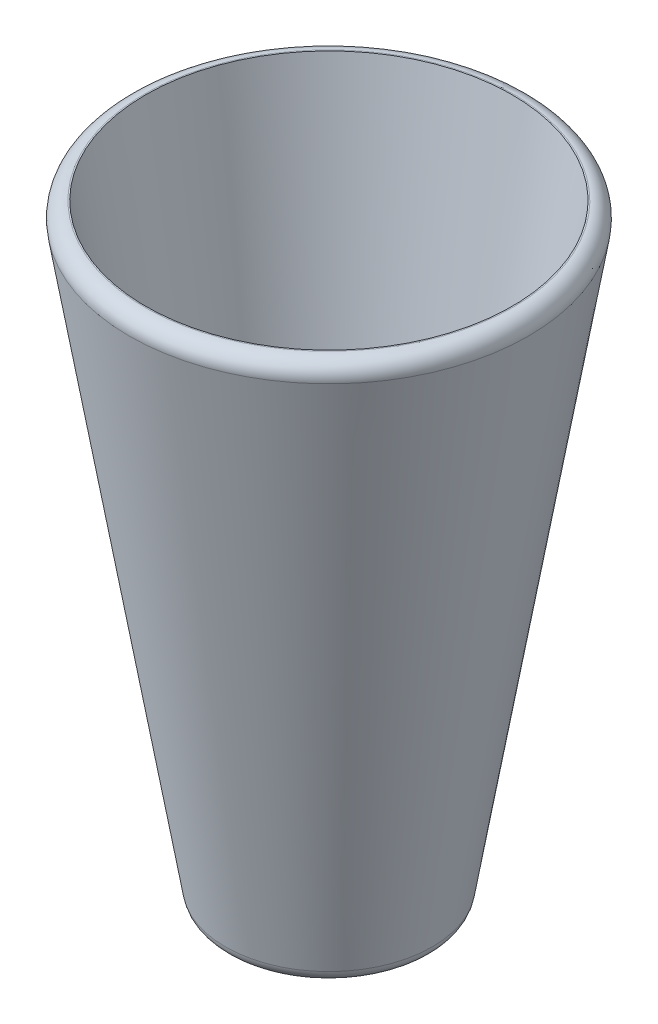
SolidWorks part; units mm, degrees
ref_plane "Front Plane" through (0, 0, 0) normal (0, 0, 1) x (1, 0, 0)
ref_plane "Top Plane" through (0, 0, 0) normal (0, 1, 0) x (1, 0, 0)
ref_plane "Right Plane" through (0, 0, 0) normal (1, 0, 0) x (0, 0, -1)
sketch "Sketch1" plane through (0, 0, 0) normal (0, 0, 1) x (1, 0, 0)
  line L0 (0, -350.5906) -> (0, -380.8417)
  line L1 (0, -380.8417) -> (200, -380.8417)
  line L2 (200, -380.8417) -> (400, 819.1583)
  line L3 (400, 819.1583) -> (362.0656, 819.1583)
  line L8 (0, -350.5906) -> (167.1074, -350.5906)
  line L9 (167.1074, -350.5906) -> (362.0656, 819.1583)
  dimension "D3" = 200
revolve "Revolve1" add sketch "Sketch1" angle 360 about L0
fillet "Fillet1" radius 30 2 edges at (-200, -380.8417, 0) (-400, 819.1583, 0)
